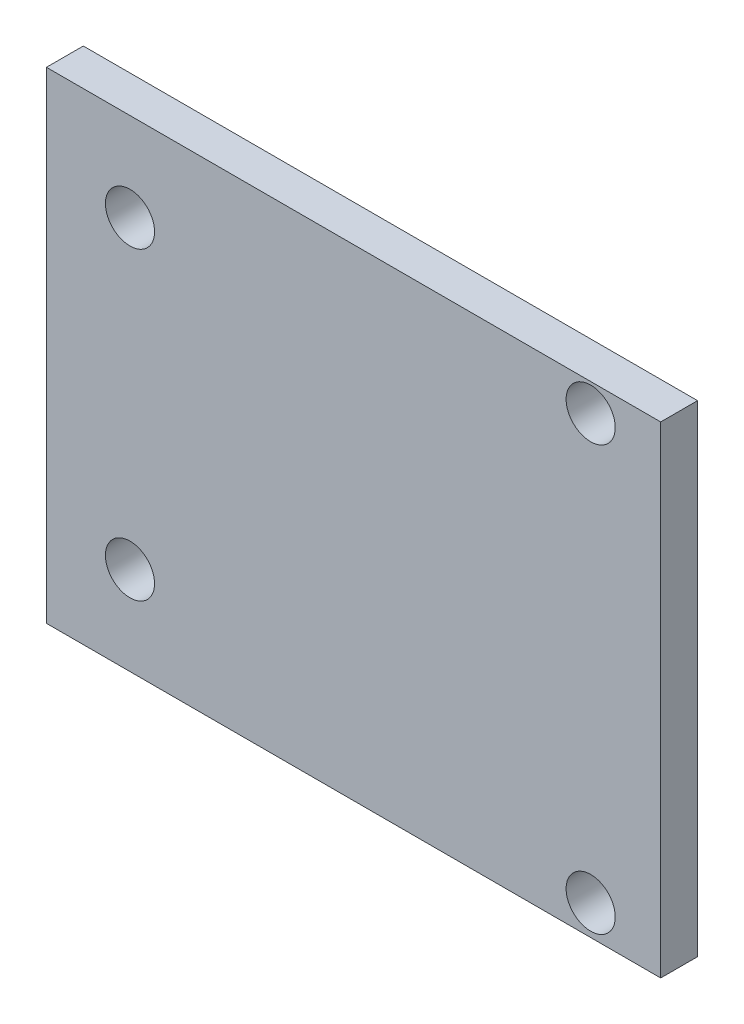
SolidWorks part; units mm, degrees
ref_plane "Front Plane" through (0, 0, 0) normal (0, 0, 1) x (1, 0, 0)
ref_plane "Top Plane" through (0, 0, 0) normal (0, 1, 0) x (1, 0, 0)
ref_plane "Right Plane" through (0, 0, 0) normal (1, 0, 0) x (0, 0, -1)
sketch "Sketch1" plane through (0, 0, 0) normal (0, 0, 1) x (1, 0, 0)
  line L0 (-25, 0) -> (25, 0) construction
  line L1 (-25, 19.6) -> (25, 19.6)
  line L2 (-25, 19.6) -> (-25, -19.6)
  line L3 (-25, -19.6) -> (25, -19.6)
  line L4 (25, 19.6) -> (25, -19.6)
  line L5 (-25, 19.6) -> (25, -19.6) construction
  line L6 (-25, -19.6) -> (25, 19.6) construction
  circle A0 centre (-18.2, -12.4) radius 2
  circle A1 centre (-18.2, 12.4) radius 2
  circle A2 centre (19.3, -17.15) radius 2
  circle A3 centre (19.3, 17.35) radius 2
  point P0 (0, 0)
  point P16 (0, 0)
  dimension "D3" = 6.8
  dimension "D4" = 4
  dimension "D6" = 4
  dimension "D9" = 2.45
  dimension "D10" = 4
  dimension "D11" = 34.5
  dimension "D1" = 39.2
  dimension "D2" = 50
  dimension "D5" = 24.8
  dimension "D7" = 37.5
  dimension "D8" = 7.2
extrude "Boss-Extrude1" add sketch "Sketch1" along normal blind 3
